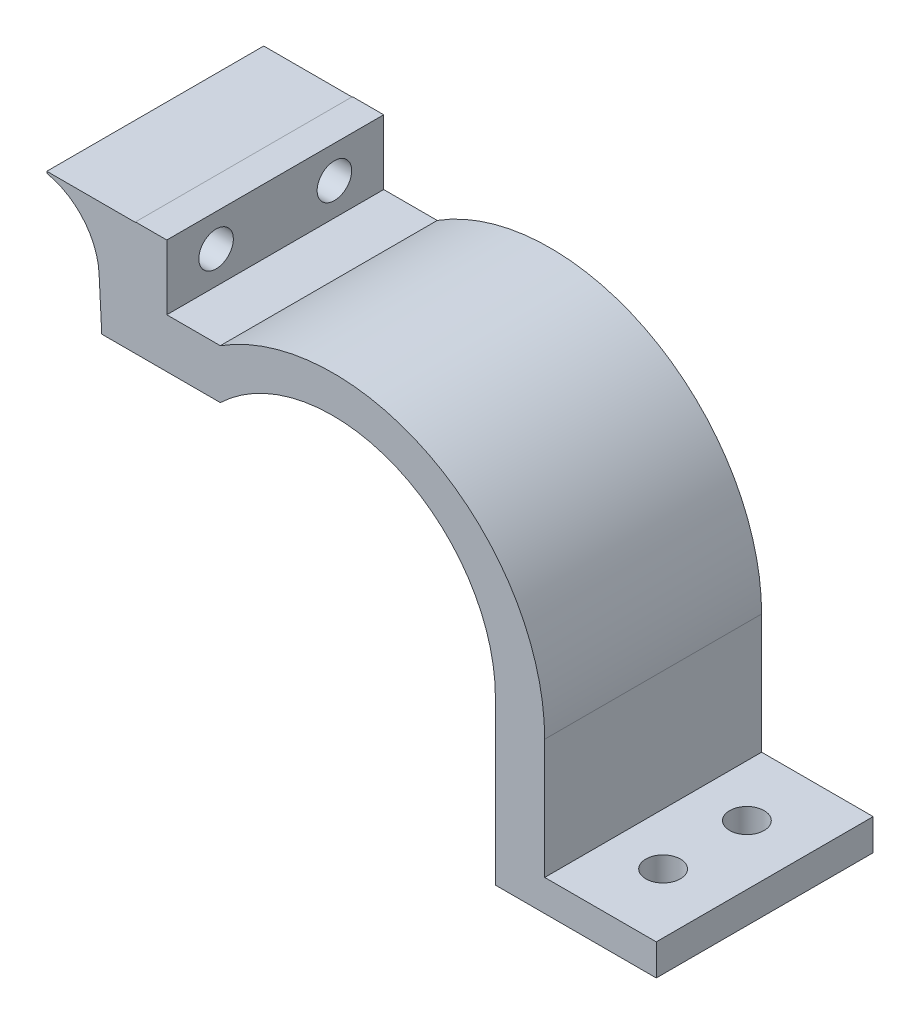
SolidWorks part; units mm, degrees
material "PETG"
ref_plane "Front Plane" through (0, 0, 0) normal (0, 0, 1) x (1, 0, 0)
ref_plane "Top Plane" through (0, 0, 0) normal (0, 1, 0) x (1, 0, 0)
ref_plane "Right Plane" through (0, 0, 0) normal (1, 0, 0) x (0, 0, -1)
sketch "Sketch1" plane through (0, 0, 0) normal (0, 0, 1) x (1, 0, 0)
  line L0 (0, 0) -> (33.0033, 0) construction
  line L1 (33.0033, 0) -> (33.0033, -33)
  line L2 (33.0033, -33) -> (0, -33) construction
  line L3 (33.0033, -33) -> (65.6321, -33)
  line L4 (65.6321, -33) -> (65.6321, -26.65)
  line L5 (65.6321, -26.65) -> (43.0033, -26.65)
  line L6 (43.0033, -26.65) -> (43.0033, -2.3696)
  line L7 (0, 0) -> (-40, 0) construction
  line L8 (-40, 0) -> (-40, 50.6526) construction
  line L9 (-22.7938, 23.8598) -> (-40, 23.8598)
  line L10 (-40, 23.8598) -> (-40, 46.9951)
  line L11 (-40, 46.9951) -> (-33.65, 46.9951)
  line L12 (-33.65, 46.9951) -> (-33.65, 33.8598)
  line L13 (-33.65, 33.8598) -> (-22.7938, 33.8598)
  circle A0 centre (0, 0) radius 33 construction
  arc A1 (-22.7938, 23.8598) -> (33.0033, 0) centre (0.0033, 0) cw
  arc A2 (-22.7938, 33.8598) -> (43.0033, -2.3696) centre (0.1304, -2.3696) cw
  dimension "D1" = 10
  dimension "D4" = 33
  dimension "D2" = 6.35
  dimension "D3" = 6.35
  dimension "10" = 10
  dimension "D5" = 40
  dimension "D6" = 32.6288
  dimension "D7" = 23.1354
extrude "Boss-Extrude1" add sketch "Sketch1" against normal blind 44
sketch "Sketch2" plane through (0, -26.65, 0) normal (0, 1, 0) x (1, 0, 0)
  line L0 (53.5164, 34) -> (53.5164, 44) construction
  line L1 (65.6321, 44) -> (43.0033, 44) construction
  line L2 (53.5164, 10) -> (53.5164, 0) construction
  line L3 (65.6321, 0) -> (43.0033, 0) construction
  circle A0 centre (53.5164, 13.5) radius 3.5
  circle A2 centre (53.5164, 30.5) radius 3.5
extrude "Cut-Extrude1" cut sketch "Sketch2" against normal up to next
sketch "Sketch4" plane through (0, 0, 0) normal (0, 0, 1) x (1, 0, 0)
  line L0 (-40, 23.8598) -> (-46.8386, 23.8598)
  line L1 (-47.3809, 34.2065) -> (-44.4795, -21.1542) construction
  line L2 (-46.8386, 23.8598) -> (-47.3809, 34.2065)
  line L4 (-47.3764, 46.9048) -> (-40, 46.9048)
  line L5 (-40, 46.9951) -> (-40, 23.8598) construction
  line L6 (-40, 46.9048) -> (-40, 23.8598)
  line L7 (-47.3764, 46.9048) -> (-57.9858, 46.9048)
  line L8 (-57.9858, 46.9048) -> (-57.9858, 46.5446)
  arc A0 (-57.9858, 46.5446) -> (-47.3809, 34.2065) centre (-60.6709, 33.51) cw
extrude "Boss-Extrude2" add sketch "Sketch4" against normal up to surface (44 mm away) up to face at (9.0807, 10.4678, -44)
sketch "Sketch5" plane through (-33.65, 0, 0) normal (1, 0, 0) x (0, 0, -1)
  line L0 (0, 33.8598) -> (0, 46.9951) construction
  line L1 (44, 33.8598) -> (44, 46.9951) construction
  line L2 (44, 46.9951) -> (0, 46.9951) construction
  circle A0 centre (10, 40.4251) radius 3.5
  circle A1 centre (34, 40.4251) radius 3.5
  dimension "D1" = 7
  dimension "D2" = 7
  dimension "D3" = 10
  dimension "D4" = 10
  dimension "D5" = 6.57
extrude "Cut-Extrude2" cut sketch "Sketch5" against normal up to next
ref_plane "Plane1" through (-58.65, 0, 0) normal (1, 0, 0) x (0, 0, -1)
sketch "Sketch6" plane through (-58.65, 0, 0) normal (1, 0, 0) x (0, 0, -1)
  circle A0 centre (34, 40.4251) radius 5
  circle A1 centre (10, 40.4251) radius 5
  dimension "D1" = 10
extrude "Cut-Extrude3" cut sketch "Sketch6" along normal blind 15
